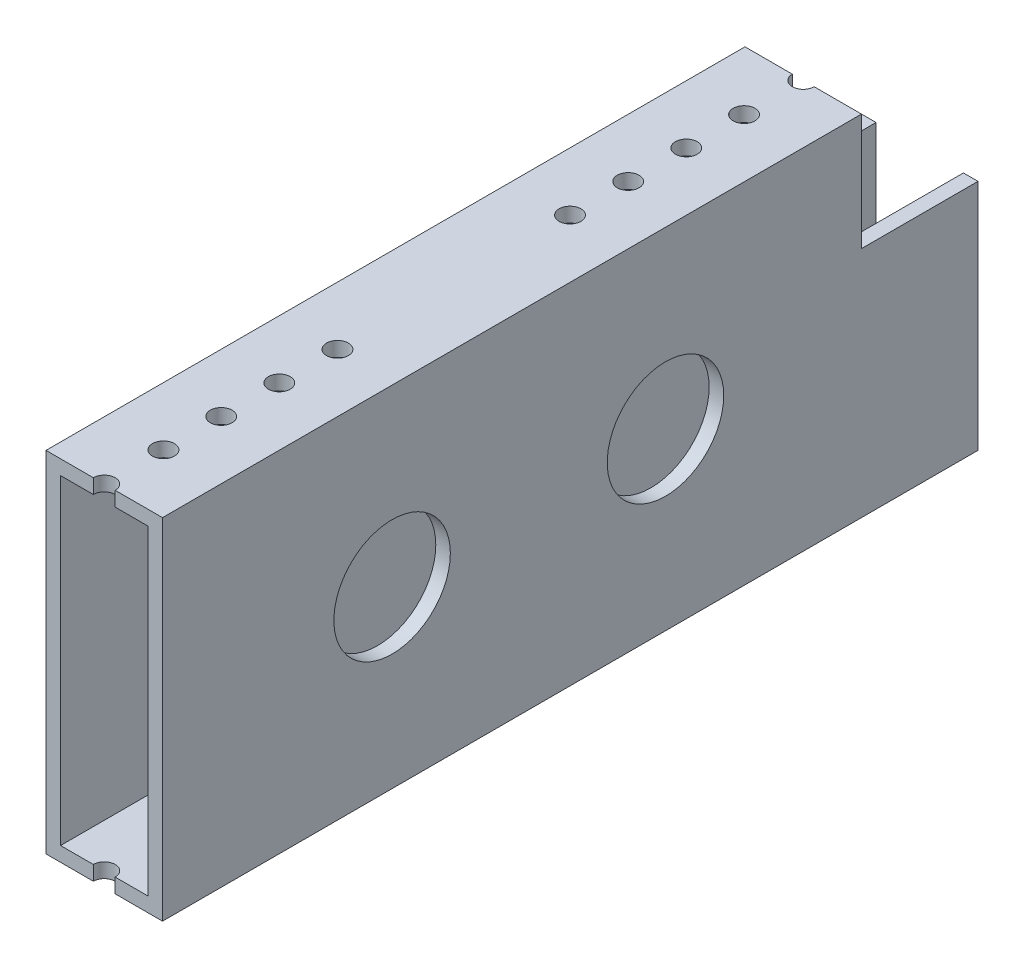
SolidWorks part; units mm, degrees
ref_plane "Front Plane" through (0, 0, 0) normal (0, 0, 1) x (1, 0, 0)
ref_plane "Top Plane" through (0, 0, 0) normal (0, 1, 0) x (1, 0, 0)
ref_plane "Right Plane" through (0, 0, 0) normal (1, 0, 0) x (0, 0, -1)
sketch "Sketch1" plane through (0, 0, 0) normal (0, 0, 1) x (1, 0, 0)
  line L1 (-12.7, -38.1) -> (12.7, -38.1)
  line L2 (-12.7, -38.1) -> (-12.7, 38.1)
  line L3 (-12.7, 38.1) -> (12.7, 38.1)
  line L4 (12.7, -38.1) -> (12.7, 38.1)
  line L5 (-12.7, -38.1) -> (12.7, 38.1) construction
  line L6 (-12.7, 38.1) -> (12.7, -38.1) construction
  point P0 (0, 0)
  dimension "D1" = 25.4
  dimension "D2" = 76.2
extrude "Boss-Extrude1" add sketch "Sketch1" along normal mid plane 177.8
shell "Shell1" thickness 3.175
sketch "Sketch2" plane through (-12.7, 0, 0) normal (-1, 0, 0) x (0, 0, 1)
  line L1 (-88.9, 38.1) -> (-63.5, 38.1)
  line L2 (-88.9, 38.1) -> (-88.9, 12.7)
  line L3 (-88.9, 12.7) -> (-63.5, 12.7)
  line L4 (-63.5, 38.1) -> (-63.5, 12.7)
  dimension "D1" = 25.4
extrude "Cut-Extrude1" cut sketch "Sketch2" against normal through all
sketch "Sketch3" plane through (0, 38.1, 0) normal (0, 1, 0) x (1, 0, 0)
  line L0 (9.525, -88.9) -> (-9.525, -88.9) construction
  line L1 (12.7, -88.9) -> (-12.7, -88.9) construction
  line L2 (-12.7, -88.9) -> (-12.7, 63.5) construction
  line L3 (-20.8214, -12.7) -> (21.7075, -12.7) construction
  circle A0 centre (0, -88.9) radius 2.3812
  circle A1 centre (0, -75.9959) radius 2.3812
  circle A2 centre (0, -63.3973) radius 2.3812
  circle A3 centre (0, -50.7315) radius 2.3812
  circle A4 centre (0, -38.0486) radius 2.3812
  circle A5 centre (0, 63.5) radius 2.3812
  circle A6 centre (0, 12.6486) radius 2.3812
  circle A7 centre (0, 25.3315) radius 2.3812
  circle A8 centre (0, 37.9973) radius 2.3812
  circle A9 centre (0, 50.5959) radius 2.3812
  point P10 (0, -88.9)
  point P15 (-12.7, -12.7)
  dimension "D1" = 4.7625
  dimension "D3" = 12.9041
  dimension "D2" = 0
  dimension "D4" = 25.5027
  dimension "D5" = 38.1685
  dimension "D6" = 50.8514
extrude "Cut-Extrude2" cut sketch "Sketch3" against normal through all
sketch "Sketch4" [suppressed] plane through (0, 38.1, 0) normal (0, 1, 0) x (1, 0, 0)
  line L2 (-12.7, -88.9) -> (-12.7, -12.7)
  line L3 (-12.7, -88.9) -> (-12.7, 63.5) construction
  line L4 (-20.5201, -12.7) -> (22.1381, -12.7) construction
sketch "Sketch5" plane through (12.7, 0, 0) normal (1, 0, 0) x (0, 0, -1)
  circle A0 centre (20.7606, 0) radius 12.7
  circle A1 centre (-38.8423, 0) radius 12.7
  dimension "D1" = 25.4
  dimension "D2" = 25.4
  dimension "D3" = 25.4
extrude "Cut-Extrude3" cut sketch "Sketch5" against normal through all
